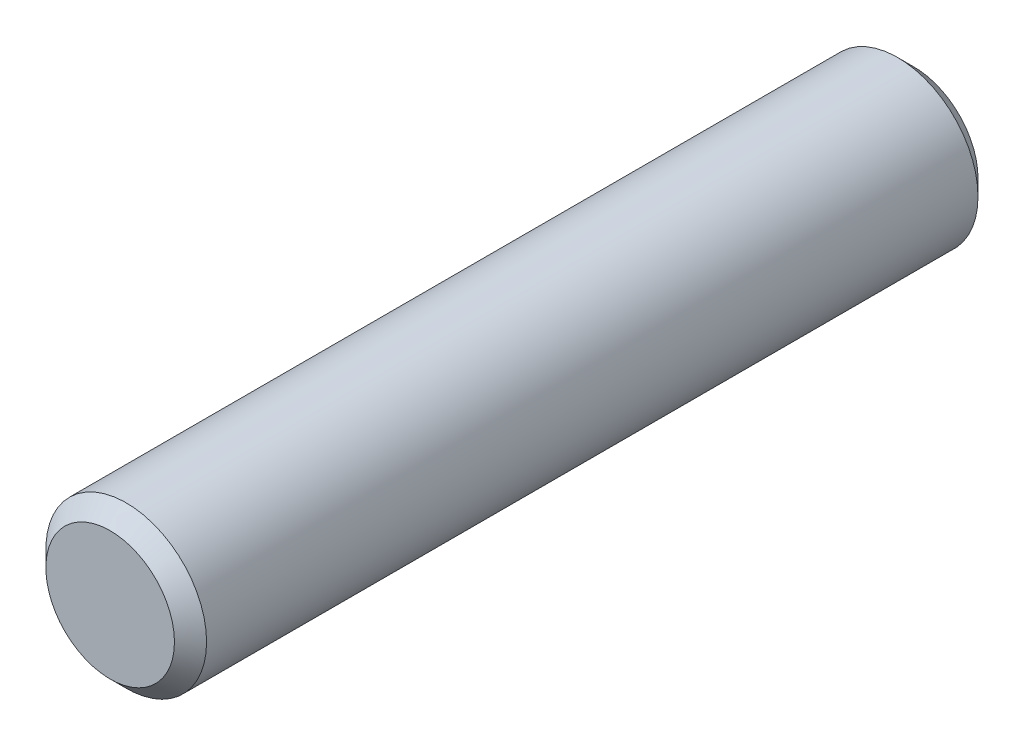
SolidWorks part; units mm, degrees
ref_plane "前视基准面" through (0, 0, 0) normal (0, 0, 1) x (1, 0, 0)
ref_plane "上视基准面" through (0, 0, 0) normal (0, 1, 0) x (1, 0, 0)
ref_plane "右视基准面" through (0, 0, 0) normal (1, 0, 0) x (0, 0, -1)
sketch "草图1" plane through (0, 0, 0) normal (0, 0, 1) x (1, 0, 0)
  circle A0 centre (0, 0) radius 1
  dimension "D1" = 2
extrude "凸台-拉伸1" add sketch "草图1" along normal mid plane 10
chamfer "倒角1" distance 0.2 angle 45 2 edges at (1, 0, -5) (1, 0, 5)
